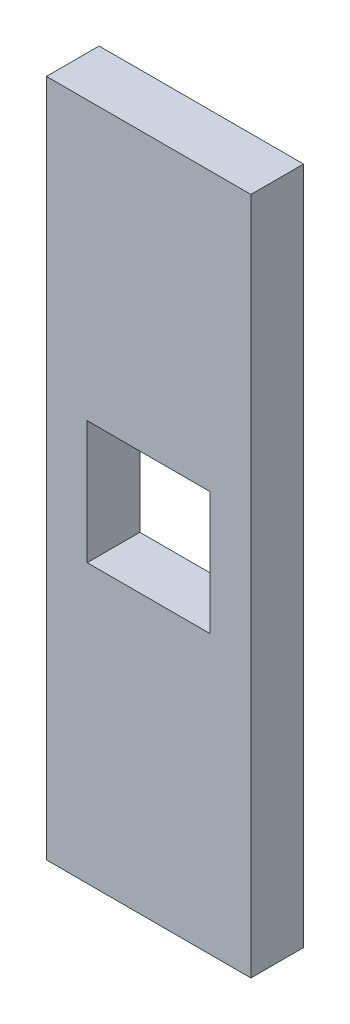
SolidWorks part; units mm, degrees
ref_plane "Front Plane" through (0, 0, 0) normal (0, 0, 1) x (1, 0, 0)
ref_plane "Top Plane" through (0, 0, 0) normal (0, 1, 0) x (1, 0, 0)
ref_plane "Right Plane" through (0, 0, 0) normal (1, 0, 0) x (0, 0, -1)
sketch "Sketch1" plane through (0, 0, 0) normal (0, 0, 1) x (1, 0, 0)
  line L0 (0, 66.85) -> (0, 44.55) construction
  line L1 (0, 66.85) -> (20, 66.85) construction
  line L2 (0, 44.55) -> (0, 39.4) construction
  line L3 (20, 0) -> (0, 0) construction
  line L4 (4.025, 39.4) -> (15.975, 39.4) construction
  line L5 (4.025, 27.45) -> (15.975, 27.45) construction
  line L6 (4.025, 39.4) -> (4.025, 27.45) construction
  line L7 (15.975, 39.4) -> (15.975, 27.45) construction
  line L8 (0, 44.55) -> (20, 44.55) construction
  line L9 (0, 39.4) -> (20, 39.4) construction
  line L10 (0, 39.4) -> (0, 27.45) construction
  line L11 (0, 27.45) -> (0, 22.3) construction
  line L12 (20, 44.55) -> (20, 39.4) construction
  line L13 (20, 66.85) -> (20, 44.55) construction
  line L14 (0, 22.3) -> (0, 0) construction
  line L15 (20, 39.4) -> (20, 27.45) construction
  line L16 (20, 27.45) -> (20, 22.3) construction
  line L17 (20, 22.3) -> (20, 0) construction
  line L18 (0, 27.45) -> (20, 27.45) construction
  line L19 (20, 22.3) -> (0, 22.3) construction
  line L20 (10, -0.0005) -> (10, 4.0956) construction
  line L21 (-0.1, 66.95) -> (20.1, 66.95)
  line L22 (20.1, 66.95) -> (20.1, 44.55)
  line L23 (20.1, 44.55) -> (20.1, 39.4)
  line L24 (20.1, 39.4) -> (20.1, 27.45)
  line L25 (20.1, 27.45) -> (20.1, 22.3)
  line L26 (20.1, 22.3) -> (20.1, -0.1)
  line L27 (20.1, -0.1) -> (-0.1, -0.1)
  line L28 (-0.1, 22.3) -> (-0.1, -0.1)
  line L29 (-0.1, 27.45) -> (-0.1, 22.3)
  line L30 (-0.1, 39.4) -> (-0.1, 27.45)
  line L31 (-0.1, 44.55) -> (-0.1, 39.4)
  line L32 (-0.1, 66.95) -> (-0.1, 44.55)
  line L33 (3.925, 39.5) -> (16.075, 39.5)
  line L34 (16.075, 39.5) -> (16.075, 27.35)
  line L35 (3.925, 27.35) -> (16.075, 27.35)
  line L36 (3.925, 39.5) -> (3.925, 27.35)
  point P18 (10, 27.45)
  point P20 (10, 39.4)
  point P21 (10, 66.85)
  dimension "D1" = 22.3
  dimension "D2" = 11.95
  dimension "D3" = 5.15
  dimension "D4" = 20
  dimension "D5" = 11.95
  dimension "D6" = 11.95
  dimension "D7" = 0.1
  dimension "D8" = 0.1
extrude "Boss-Extrude1" add sketch "Sketch1" along normal blind 5.2
